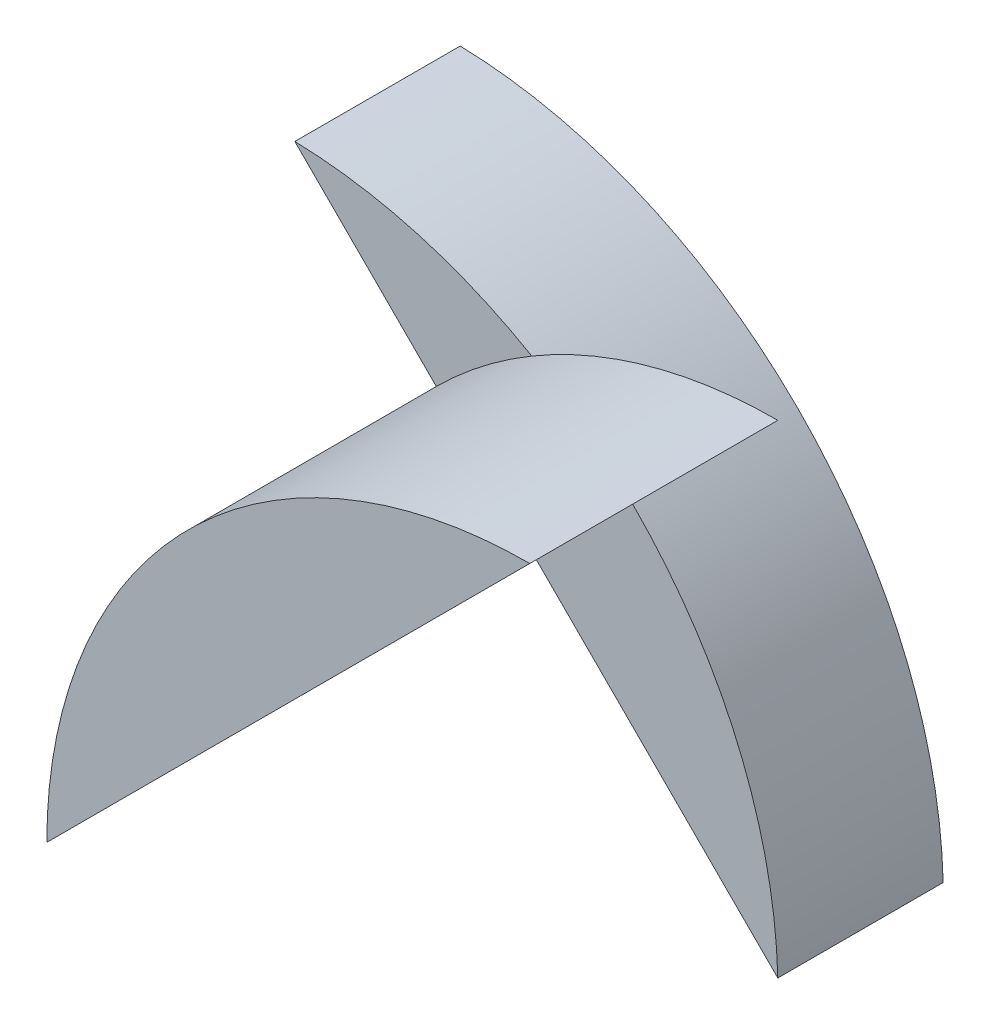
SolidWorks part; units mm, degrees
ref_plane "Front Plane" through (0, 0, 0) normal (0, 0, 1) x (1, 0, 0)
ref_plane "Top Plane" through (0, 0, 0) normal (0, 1, 0) x (1, 0, 0)
ref_plane "Right Plane" through (0, 0, 0) normal (1, 0, 0) x (0, 0, -1)
sketch "Sketch1" plane through (0, 0, 0) normal (0, 0, 1) x (1, 0, 0)
  line L0 (-74.0257, 30.8188) -> (-44.8152, 1.6083)
  arc A0 (-74.0257, 30.8188) -> (-44.8152, 1.6083) centre (-74.8152, 0.8188) cw
  dimension "30" = 30
  dimension "D2" = 30
extrude "Boss-Extrude1" add sketch "Sketch1" along normal blind 10
sketch "Sketch3" plane through (0, 0, 10) normal (0, 0, 1) x (1, 0, 0)
  line L0 (-74.0257, 1.6083) -> (-44.8152, 30.8188)
  arc A0 (-74.0257, 1.6083) -> (-44.8152, 30.8188) centre (-44.8152, 1.6083) cw
extrude "Boss-Extrude2" add sketch "Sketch3" along normal blind 15
